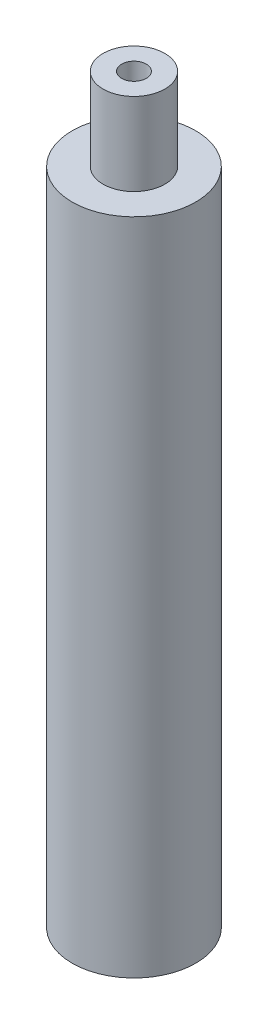
SolidWorks part; units mm, degrees
ref_plane "Front Plane" through (0, 0, 0) normal (0, 0, 1) x (1, 0, 0)
ref_plane "Top Plane" through (0, 0, 0) normal (0, 1, 0) x (1, 0, 0)
ref_plane "Right Plane" through (0, 0, 0) normal (1, 0, 0) x (0, 0, -1)
sketch "Sketch1" plane through (0, 0, 0) normal (0, 1, 0) x (1, 0, 0)
  circle A0 centre (0, 0) radius 9.525
  dimension "D1" = 19.05
extrude "Boss-Extrude2" add sketch "Sketch1" along normal blind 101.6
sketch "Sketch3" plane through (0, 101.6, 0) normal (0, 1, 0) x (1, 0, 0)
  circle A0 centre (0, 0) radius 4.7625
  dimension "D1" = 9.525
extrude "Boss-Extrude3" add sketch "Sketch3" along normal blind 12.7
sketch "Sketch14" plane through (0, 0, 0) normal (0, -1, 0) x (1, 0, 0)
  circle A0 centre (0, 0) radius 5.7547
  dimension "D1" = 11.5094
extrude "Cut-Extrude4" cut sketch "Sketch14" against normal blind 25.4
sketch "Sketch17" plane through (0, 25.4, 0) normal (0, -1, 0) x (1, 0, 0)
  circle A0 centre (0, 0) radius 1.905
  dimension "D1" = 3.81
extrude "Cut-Extrude5" cut sketch "Sketch17" against normal through all
